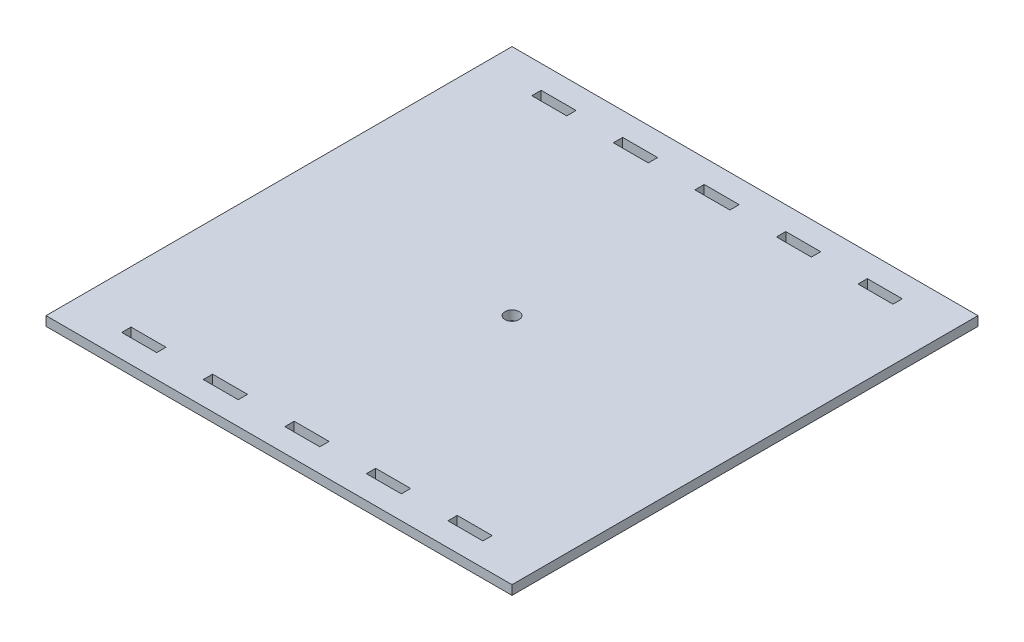
SolidWorks part; units mm, degrees
material "1060 Alloy"
ref_plane "Front Plane" through (0, 0, 0) normal (0, 0, 1) x (1, 0, 0)
ref_plane "Top Plane" through (0, 0, 0) normal (0, 1, 0) x (1, 0, 0)
ref_plane "Right Plane" through (0, 0, 0) normal (1, 0, 0) x (0, 0, -1)
sketch "Sketch1" plane through (0, 0, 0) normal (0, 1, 0) x (1, 0, 0)
  line L0 (0, -100) -> (200, -100) construction
  line L1 (0, 0) -> (200, 0)
  line L2 (0, 0) -> (0, -200)
  line L3 (0, -200) -> (200, -200)
  line L4 (200, 0) -> (200, -200)
  line L5 (22.5, -10) -> (37.5, -10)
  line L6 (22.5, -10) -> (22.5, -14)
  line L7 (22.5, -14) -> (37.5, -14)
  line L8 (37.5, -10) -> (37.5, -14)
  line L9 (57.5, -10) -> (72.5, -10)
  line L10 (57.5, -10) -> (57.5, -14)
  line L11 (57.5, -14) -> (72.5, -14)
  line L12 (72.5, -10) -> (72.5, -14)
  line L13 (92.5, -10) -> (107.5, -10)
  line L14 (92.5, -10) -> (92.5, -14)
  line L15 (92.5, -14) -> (107.5, -14)
  line L16 (107.5, -10) -> (107.5, -14)
  line L17 (127.5, -10) -> (142.5, -10)
  line L18 (127.5, -10) -> (127.5, -14)
  line L19 (127.5, -14) -> (142.5, -14)
  line L20 (142.5, -10) -> (142.5, -14)
  line L21 (162.5, -10) -> (177.5, -10)
  line L22 (162.5, -10) -> (162.5, -14)
  line L23 (162.5, -14) -> (177.5, -14)
  line L24 (177.5, -10) -> (177.5, -14)
  line L25 (177.5, -190) -> (177.5, -186)
  line L26 (162.5, -186) -> (177.5, -186)
  line L27 (162.5, -190) -> (162.5, -186)
  line L28 (162.5, -190) -> (177.5, -190)
  line L29 (142.5, -190) -> (142.5, -186)
  line L30 (127.5, -186) -> (142.5, -186)
  line L31 (127.5, -190) -> (127.5, -186)
  line L32 (127.5, -190) -> (142.5, -190)
  line L33 (107.5, -190) -> (107.5, -186)
  line L34 (92.5, -186) -> (107.5, -186)
  line L35 (92.5, -190) -> (92.5, -186)
  line L36 (92.5, -190) -> (107.5, -190)
  line L37 (72.5, -190) -> (72.5, -186)
  line L38 (57.5, -186) -> (72.5, -186)
  line L39 (57.5, -190) -> (57.5, -186)
  line L40 (57.5, -190) -> (72.5, -190)
  line L41 (37.5, -190) -> (37.5, -186)
  line L42 (22.5, -186) -> (37.5, -186)
  line L43 (22.5, -190) -> (22.5, -186)
  line L44 (22.5, -190) -> (37.5, -190)
  circle A0 centre (100, -100) radius 3
  point P47 (30, -10)
  dimension "D1" = 200
  dimension "D2" = 200
  dimension "D3" = 15
  dimension "D4" = 4
  dimension "D5" = 4
  dimension "D6" = 4
  dimension "D7" = 4
  dimension "D8" = 4
  dimension "D9" = 15
  dimension "D10" = 15
  dimension "D11" = 15
  dimension "D12" = 15
  dimension "D13" = 22.5
  dimension "D14" = 22.5
  dimension "D15" = 20
  dimension "D16" = 20
  dimension "D17" = 20
  dimension "D18" = 20
  dimension "D19" = 10
extrude "Boss-Extrude1" add sketch "Sketch1" along normal blind 4
